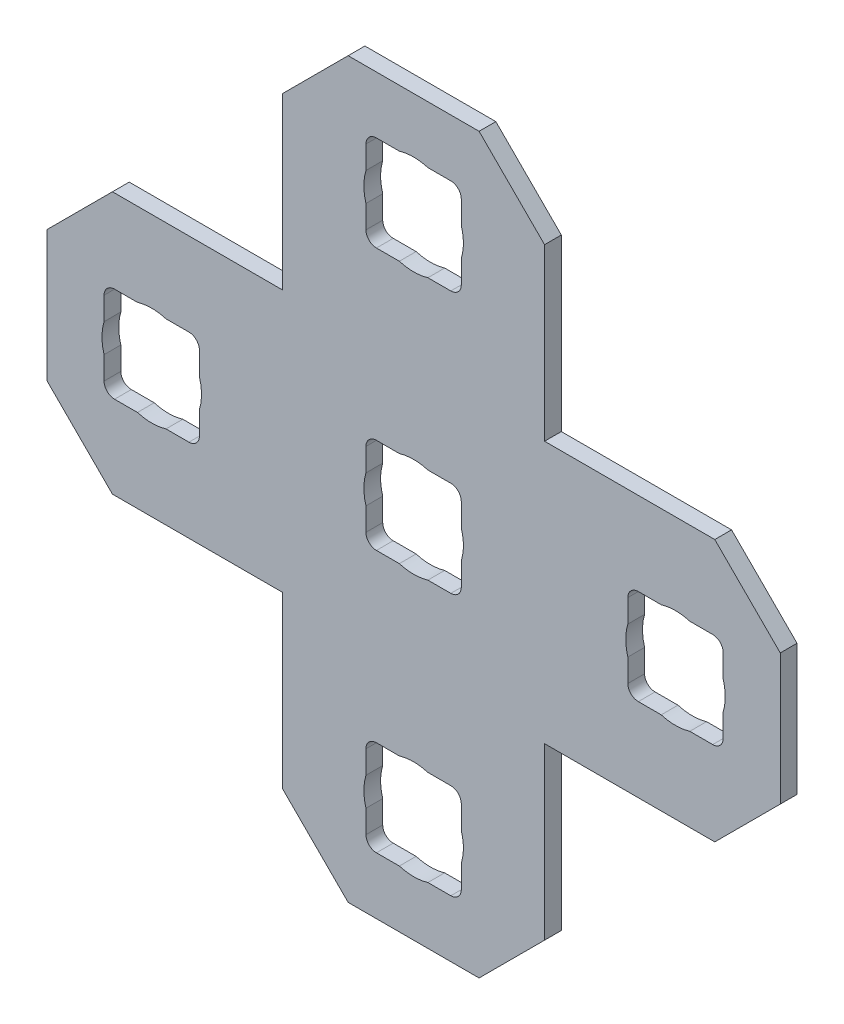
SolidWorks part; units mm, degrees
material "Custom Plastic"
ref_plane "Front Plane" through (0, 0, 0) normal (0, 0, 1) x (1, 0, 0)
ref_plane "Top Plane" through (0, 0, 0) normal (0, 1, 0) x (1, 0, 0)
ref_plane "Right Plane" through (0, 0, 0) normal (1, 0, 0) x (0, 0, -1)
ref_plane "Plane1" through (0, 0, 0) normal (0, 0, -1) x (-1, 0, 0)
sketch "Sketch1" plane through (0, 0, 0) normal (0, 0, -1) x (-1, 0, 0)
  line L0 (8.3857, -18.8455) -> (5.2107, -15.6705)
  line L1 (5.2107, -15.6705) -> (-3.0443, -15.6705)
  line L2 (-3.0443, -15.6705) -> (-3.0443, -7.4155)
  line L3 (-3.0443, -7.4155) -> (-6.2193, -4.2405)
  line L4 (-6.2193, -4.2405) -> (-12.5693, -4.2405)
  line L5 (-12.5693, -4.2405) -> (-15.7443, -7.4155)
  line L6 (-15.7443, -7.4155) -> (-15.7443, -15.6705)
  line L7 (-15.7443, -15.6705) -> (-23.9993, -15.6705)
  line L8 (-23.9993, -15.6705) -> (-27.1743, -18.8455)
  line L9 (-27.1743, -18.8455) -> (-27.1743, -25.1955)
  line L10 (-27.1743, -25.1955) -> (-23.9993, -28.3705)
  line L11 (-23.9993, -28.3705) -> (-15.7443, -28.3705)
  line L12 (-15.7443, -28.3705) -> (-15.7443, -36.6255)
  line L13 (-15.7443, -36.6255) -> (-12.5693, -39.8005)
  line L14 (-12.5693, -39.8005) -> (-6.2193, -39.8005)
  line L15 (-6.2193, -39.8005) -> (-3.0443, -36.6255)
  line L16 (-3.0443, -36.6255) -> (-3.0443, -28.3705)
  line L17 (-3.0443, -28.3705) -> (5.2107, -28.3705)
  line L18 (5.2107, -28.3705) -> (8.3857, -25.1955)
  line L19 (8.3857, -25.1955) -> (8.3857, -18.8455)
  line L20 (5.1091, -24.3319) -> (1.5023, -24.3319)
  line L21 (0.9943, -23.8239) -> (0.9943, -20.2171)
  line L22 (1.5023, -19.7091) -> (5.1091, -19.7091)
  line L23 (5.6171, -20.2171) -> (5.6171, -23.8239)
  line L24 (-7.5909, -24.3319) -> (-11.1977, -24.3319)
  line L25 (-11.7057, -23.8239) -> (-11.7057, -20.2171)
  line L26 (-11.1977, -19.7091) -> (-7.5909, -19.7091)
  line L27 (-7.0829, -20.2171) -> (-7.0829, -23.8239)
  line L28 (-11.1977, -7.0091) -> (-7.5909, -7.0091)
  line L29 (-7.0829, -7.5171) -> (-7.0829, -11.1239)
  line L30 (-7.5909, -11.6319) -> (-11.1977, -11.6319)
  line L31 (-11.7057, -11.1239) -> (-11.7057, -7.5171)
  line L32 (-20.2909, -24.3319) -> (-23.8977, -24.3319)
  line L33 (-24.4057, -23.8239) -> (-24.4057, -20.2171)
  line L34 (-23.8977, -19.7091) -> (-20.2909, -19.7091)
  line L35 (-19.7829, -20.2171) -> (-19.7829, -23.8239)
  line L36 (-11.7057, -36.5239) -> (-11.7057, -32.9171)
  line L37 (-11.1977, -32.4091) -> (-7.5909, -32.4091)
  line L38 (-7.0829, -32.9171) -> (-7.0829, -36.5239)
  line L39 (-7.5909, -37.0319) -> (-11.1977, -37.0319)
  arc A0 (1.5023, -24.3319) -> (0.9943, -23.8239) centre (1.5023, -23.8239) cw
  arc A1 (0.9943, -20.2171) -> (1.5023, -19.7091) centre (1.5023, -20.2171) cw
  arc A2 (5.1091, -19.7091) -> (5.6171, -20.2171) centre (5.1091, -20.2171) cw
  arc A3 (5.6171, -23.8239) -> (5.1091, -24.3319) centre (5.1091, -23.8239) cw
  arc A4 (-11.1977, -24.3319) -> (-11.7057, -23.8239) centre (-11.1977, -23.8239) cw
  arc A5 (-11.7057, -20.2171) -> (-11.1977, -19.7091) centre (-11.1977, -20.2171) cw
  arc A6 (-7.5909, -19.7091) -> (-7.0829, -20.2171) centre (-7.5909, -20.2171) cw
  arc A7 (-7.0829, -23.8239) -> (-7.5909, -24.3319) centre (-7.5909, -23.8239) cw
  arc A8 (-7.5909, -7.0091) -> (-7.0829, -7.5171) centre (-7.5909, -7.5171) cw
  arc A9 (-7.0829, -11.1239) -> (-7.5909, -11.6319) centre (-7.5909, -11.1239) cw
  arc A10 (-11.1977, -11.6319) -> (-11.7057, -11.1239) centre (-11.1977, -11.1239) cw
  arc A11 (-11.7057, -7.5171) -> (-11.1977, -7.0091) centre (-11.1977, -7.5171) cw
  arc A12 (-23.8977, -24.3319) -> (-24.4057, -23.8239) centre (-23.8977, -23.8239) cw
  arc A13 (-24.4057, -20.2171) -> (-23.8977, -19.7091) centre (-23.8977, -20.2171) cw
  arc A14 (-20.2909, -19.7091) -> (-19.7829, -20.2171) centre (-20.2909, -20.2171) cw
  arc A15 (-19.7829, -23.8239) -> (-20.2909, -24.3319) centre (-20.2909, -23.8239) cw
  arc A16 (-11.7057, -32.9171) -> (-11.1977, -32.4091) centre (-11.1977, -32.9171) cw
  arc A17 (-7.5909, -32.4091) -> (-7.0829, -32.9171) centre (-7.5909, -32.9171) cw
  arc A18 (-7.0829, -36.5239) -> (-7.5909, -37.0319) centre (-7.5909, -36.5239) cw
  arc A19 (-11.1977, -37.0319) -> (-11.7057, -36.5239) centre (-11.1977, -36.5239) cw
extrude "Boss-Extrude1" add sketch "Sketch1" against normal blind 0.8128
sketch "Sketch2" plane through (0, 0, 0.8128) normal (0, 0, 1) x (1, 0, 0)
  line L0 (-5.6171, -22.0205) -> (-0.9943, -22.0205) construction
  line L1 (-5.6171, -23.8239) -> (-5.6171, -20.2171) construction
  line L2 (-0.9943, -20.2171) -> (-0.9943, -23.8239) construction
  line L4 (7.0829, -11.1239) -> (7.0829, -7.5171) construction
  line L5 (7.0829, -9.3205) -> (11.7057, -9.3205) construction
  line L6 (11.7057, -7.5171) -> (11.7057, -11.1239) construction
  line L8 (20.2909, -19.7091) -> (23.8977, -19.7091) construction
  line L9 (22.0943, -19.7091) -> (22.0943, -24.3319) construction
  line L10 (23.8977, -24.3319) -> (20.2909, -24.3319) construction
  line L12 (11.7057, -32.9171) -> (11.7057, -36.5239) construction
  line L13 (11.7057, -34.7205) -> (7.0829, -34.7205) construction
  line L14 (7.0829, -36.5239) -> (7.0829, -32.9171) construction
  line L16 (11.7057, -20.2171) -> (11.7057, -23.8239) construction
  line L17 (11.7057, -22.0205) -> (7.0829, -22.0205) construction
  line L18 (7.0829, -23.8239) -> (7.0829, -20.2171) construction
  circle A0 centre (-3.3057, -22.0205) radius 2.413
  circle A1 centre (9.3943, -22.0205) radius 2.413
  circle A2 centre (9.3943, -9.3205) radius 2.413
  circle A3 centre (22.0943, -22.0205) radius 2.413
  circle A4 centre (9.3943, -34.7205) radius 2.413
  dimension "D1" = 4.826
extrude "Cut-Extrude1" cut sketch "Sketch2" against normal blind 2.54
